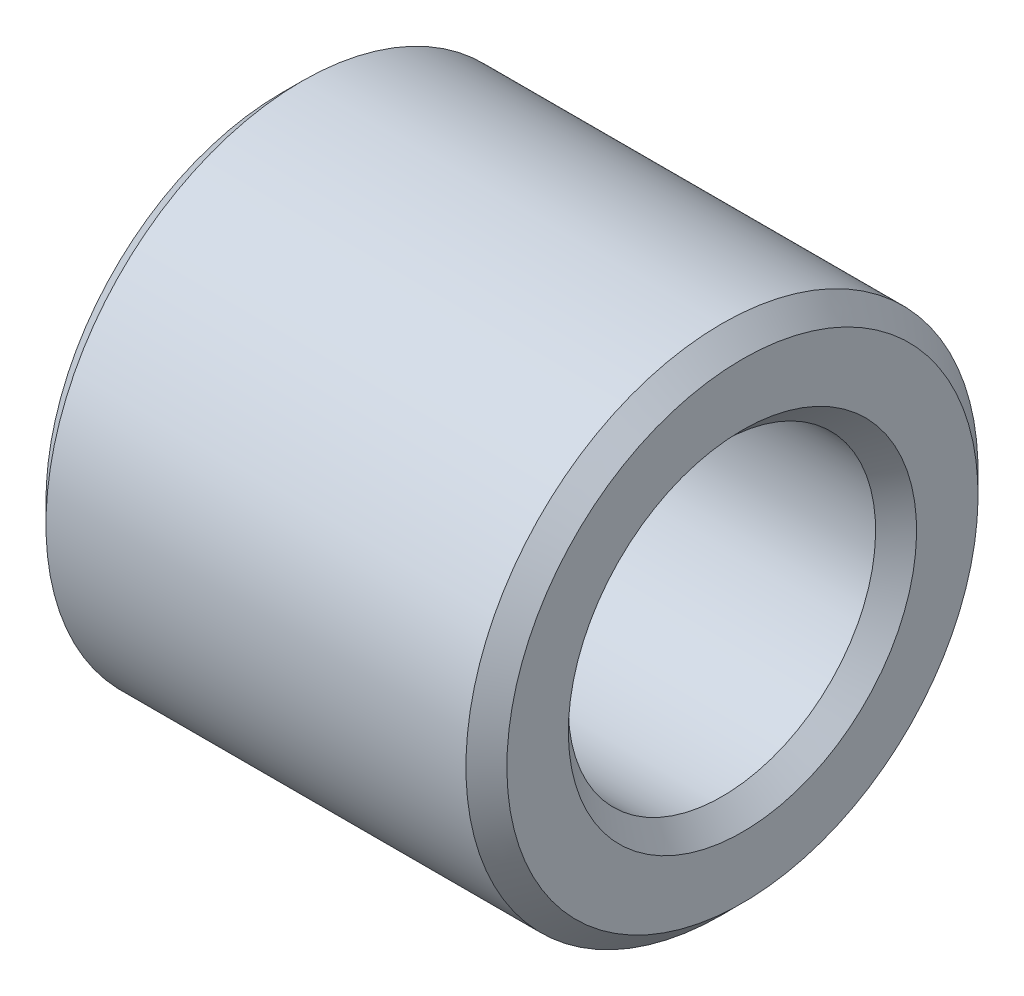
SolidWorks part; units mm, degrees
material "AISI 304"
ref_plane "正面" through (0, 0, 0) normal (0, 0, 1) x (1, 0, 0)
ref_plane "平面" through (0, 0, 0) normal (0, 1, 0) x (1, 0, 0)
ref_plane "右側面" through (0, 0, 0) normal (1, 0, 0) x (0, 0, -1)
ref_plane "Plane1" through (0, 0, 0) normal (0, 0, 1) x (1, 0, 0)
sketch "Sketch1" plane through (0, 0, 0) normal (0, 0, 1) x (1, 0, 0)
  line L0 (0, -1.7) -> (0, -2.3)
  line L1 (0, -2.3) -> (0.2, -2.5)
  line L2 (0.2, -2.5) -> (4.3, -2.5)
  line L3 (4.3, -2.5) -> (4.5, -2.3)
  line L4 (4.5, -2.3) -> (4.5, -1.7)
  line L5 (4.5, -1.7) -> (4.3, -1.5)
  line L6 (4.3, -1.5) -> (0.2, -1.5)
  line L7 (0.2, -1.5) -> (0, -1.7)
  line L8 (-3, 0) -> (3, 0) construction
revolve "Revolve1" add sketch "Sketch1" angle 360 about L8
